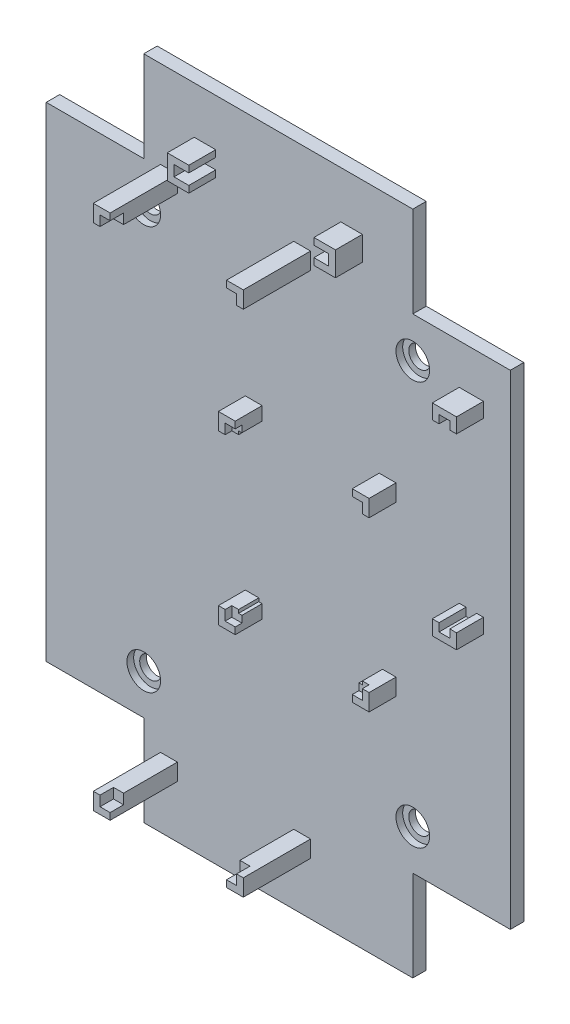
SolidWorks part; units mm, degrees
ref_plane "Front Plane" through (0, 0, 0) normal (0, 0, 1) x (1, 0, 0)
ref_plane "Top Plane" through (0, 0, 0) normal (0, 1, 0) x (1, 0, 0)
ref_plane "Right Plane" through (0, 0, 0) normal (1, 0, 0) x (0, 0, -1)
sketch3d "3DSketch1"
  line L12 (0, 85.2094, 0) -> (0, -85.2094, 0) construction
  line L13 (-20, 20.8016, 0) -> (20, 20.8016, 0)
  line L14 (20, 20.8016, 0) -> (20, 7.3016, 0)
  line L15 (20, 7.3016, 0) -> (34.5, 7.3016, 0)
  line L16 (34.5, 7.3016, 0) -> (34.5, -64.6984, 0)
  line L17 (34.5, -64.6984, 0) -> (20, -64.6984, 0)
  line L18 (20, -64.6984, 0) -> (20, -78.1984, 0)
  line L19 (20, -78.1984, 0) -> (-20, -78.1984, 0)
  line L20 (-85.4416, -28.6984, 0) -> (102.9541, -28.6984, 0) construction
  line L21 (-20, -64.6984, 0) -> (-20, -78.1984, 0)
  line L22 (-34.5, -64.6984, 0) -> (-20, -64.6984, 0)
  line L23 (-20, 7.3016, 0) -> (-34.5, 7.3016, 0)
  line L24 (-34.5, 7.3016, 0) -> (-34.5, -64.6984, 0)
  line L25 (-20, 20.8016, 0) -> (-20, 7.3016, 0)
  line L26 (0, 0, 58.811) -> (0, 0, -52.3115) construction
  circle A0 centre (-20, 1.3016, 0) radius 1.6
  circle A1 centre (20, 1.3016, 0) radius 1.6
  circle A2 centre (20, -58.6984, 0) radius 1.6
  circle A3 centre (-20, -58.6984, 0) radius 1.6
  point P15 (0, -78.1984, 0)
  point P19 (0, 20.8016, 0)
  point P21 (-20, 1.3016, 1.6)
  point P24 (20, 1.3016, 1.6)
  point P27 (20, -58.6984, 1.6)
  point P30 (-20, -58.6984, 1.6)
  dimension "D10" = 3.2
  dimension "D11" = 3.2
  dimension "D1" = 99
  dimension "D2" = 34.5
  dimension "D3" = 20
  dimension "D4" = 20
  dimension "D5" = 49.5
  dimension "D6" = 72
  dimension "D7" = 13.5
  dimension "D8" = 20
  dimension "D9" = 14.5
  dimension "D12" = 40
  dimension "D13" = 20
  dimension "D14" = 30
  dimension "D15" = 30
extrude "Boss-Extrude1" add sketch "3DSketch1" along direction (0, 0, -1) on the side against the normal blind 2 contours L21 L19 L18 L17 L16 L15 L14 L13 L25 L23 L24 L22
sketch "Sketch2" plane through (0, 0, 0) normal (0, 0, 1) x (1, 0, 0)
  line L0 (0, 0) -> (0, -83.2949) construction
  line L1 (-48.7659, -28.6984) -> (71.6911, -28.6984) construction
  line L3 (-20, 7.3016) -> (-34.5, 7.3016) construction
  circle A0 centre (-20, 1.3016) radius 1.6
  circle A1 centre (20, 1.3016) radius 1.6
  circle A2 centre (20, -58.6984) radius 1.6
  circle A3 centre (-20, -58.6984) radius 1.6
  point P0 (-20, 1.3016)
  point P10 (20, 1.3016)
  point P12 (-20, -58.6984)
  point P13 (20, -58.6984)
  dimension "D4" = 3.2
  dimension "D5" = 3.2
  dimension "D6" = 3.2
  dimension "D7" = 3.2
  dimension "D1" = 36
  dimension "D2" = 30
  dimension "D3" = 20
extrude "Cut-Extrude1" cut sketch "Sketch2" against normal blind 2
sketch "Sketch4" plane through (0, 0, 0) normal (0, 0, 1) x (1, 0, 0)
sketch "Sketch5" plane through (0, 0, 0) normal (0, 0, 1) x (1, 0, 0)
  circle A0 centre (-20, 1.3016) radius 2.5
  circle A1 centre (20, 1.3016) radius 2.5
  circle A2 centre (20, -58.6984) radius 2.5
  circle A3 centre (-20, -58.6984) radius 2.5
  dimension "D1" = 5
  dimension "D2" = 5
  dimension "D3" = 5
  dimension "D4" = 5
extrude "Cut-Extrude2" cut sketch "Sketch5" against normal blind 1
sketch "Sketch6" plane through (0, 0, 0) normal (0, 0, 1) x (1, 0, 0)
  line L1 (-11.5, 12.8016) -> (11.5, 12.8016)
  line L2 (-11.5, 12.8016) -> (-11.5, 11.2016)
  line L3 (-11.5, 11.2016) -> (11.5, 11.2016)
  line L4 (11.5, 12.8016) -> (11.5, 11.2016)
  line L5 (20, 20.8016) -> (20, 7.3016) construction
  line L6 (-20, 20.8016) -> (20, 20.8016) construction
  line L8 (-12.5, 13.8016) -> (12.5, 13.8016)
  line L9 (-12.5, 13.8016) -> (-12.5, 10.2016)
  line L10 (-12.5, 10.2016) -> (12.5, 10.2016)
  line L11 (12.5, 13.8016) -> (12.5, 10.2016)
  point P6 (11.5, 12.0016)
  point P13 (-11.5, 12.0016)
  dimension "D1" = 23
  dimension "D2" = 1.6
  dimension "D3" = 8.5
  dimension "D4" = 8
  dimension "D5" = 1
  dimension "D6" = 1
  dimension "D7" = 1
  dimension "D8" = 1
extrude "Boss-Extrude2" add sketch "Sketch6" along normal blind 4
sketch "Sketch7" plane through (0, 13.8016, 0) normal (0, 1, 0) x (1, 0, 0)
  line L0 (12.5, 0) -> (-12.5, 0) construction
  line L1 (-9.3, 0) -> (9.3, 0)
  line L2 (-9.3, 0) -> (-9.3, -4)
  line L3 (-9.3, -4) -> (9.3, -4)
  line L4 (9.3, 0) -> (9.3, -4)
  line L5 (12.5, -4) -> (-12.5, -4) construction
  line L6 (-12.5, -4) -> (-12.5, 0) construction
  line L7 (12.5, -4) -> (12.5, 0) construction
  dimension "D1" = 3.2
  dimension "D2" = 3.2
extrude "Cut-Extrude3" cut sketch "Sketch7" against normal blind 15 contours L2 L3 L4 L1
sketch "Sketch9" plane through (0, 0, 0) normal (0, 0, 1) x (1, 0, 0)
  line L0 (20, 7.3016) -> (34.5, 7.3016) construction
  line L1 (27.9, 0.3016) -> (29.5, 0.3016)
  line L2 (27.9, 0.3016) -> (27.9, -27.6984)
  line L3 (27.9, -27.6984) -> (29.5, -27.6984)
  line L4 (29.5, 0.3016) -> (29.5, -27.6984)
  line L5 (34.5, 7.3016) -> (34.5, -64.6984) construction
  line L7 (26.9, 1.3016) -> (30.5, 1.3016)
  line L8 (26.9, 1.3016) -> (26.9, -28.6984)
  line L9 (26.9, -28.6984) -> (30.5, -28.6984)
  line L10 (30.5, 1.3016) -> (30.5, -28.6984)
  point P4 (29.5, -27.6984)
  dimension "D1" = 28
  dimension "D2" = 1.6
  dimension "D3" = 35
  dimension "D4" = 5
  dimension "D5" = 1
  dimension "D6" = 1
  dimension "D7" = 1
  dimension "D8" = 1
extrude "Boss-Extrude4" add sketch "Sketch9" along normal blind 4
sketch "Sketch10" plane through (30.5, 0, 0) normal (1, 0, 0) x (0, 0, -1)
  line L0 (-4, -28.6984) -> (-4, 1.3016) construction
  line L1 (-4, -0.8984) -> (0, -0.8984)
  line L2 (-4, -0.8984) -> (-4, -26.4984)
  line L3 (-4, -26.4984) -> (0, -26.4984)
  line L4 (0, -0.8984) -> (0, -26.4984)
  line L5 (0, 7.3016) -> (0, -64.6984) construction
  line L6 (-4, 1.3016) -> (0, 1.3016) construction
  line L7 (-4, -28.6984) -> (0, -28.6984) construction
  point P10 (-2, 1.3016)
  dimension "D1" = 2.2
  dimension "D2" = 2.2
extrude "Cut-Extrude4" cut sketch "Sketch10" against normal blind 4
sketch "Sketch11" plane through (0, 0, 0) normal (0, 0, 1) x (1, 0, 0)
  line L0 (34.5, 7.3016) -> (34.5, -64.6984) construction
  line L1 (-3.9, -16.6984) -> (16.5, -16.6984)
  line L2 (-3.9, -16.6984) -> (-3.9, -42.1984)
  line L3 (-3.9, -42.1984) -> (16.5, -42.1984)
  line L4 (16.5, -16.6984) -> (16.5, -42.1984)
  line L5 (20, -78.1984) -> (-20, -78.1984) construction
  line L7 (-4.9, -15.6984) -> (17.5, -15.6984)
  line L8 (-4.9, -15.6984) -> (-4.9, -43.1984)
  line L9 (-4.9, -43.1984) -> (17.5, -43.1984)
  line L10 (17.5, -15.6984) -> (17.5, -43.1984)
  dimension "D1" = 25.5
  dimension "D2" = 20.4
  dimension "D3" = 18
  dimension "D4" = 36
  dimension "D5" = 1
  dimension "D6" = 1
  dimension "D7" = 1
  dimension "D8" = 1
extrude "Boss-Extrude5" add sketch "Sketch11" along normal blind 4
sketch "Sketch12" plane through (0, 0, 0) normal (0, 0, 1) x (1, 0, 0)
  line L9 (-3.9, -16.6984) -> (16.5, -16.6984)
  line L10 (-3.9, -16.6984) -> (-3.9, -42.1984)
  line L11 (-3.9, -42.1984) -> (16.5, -42.1984)
  line L12 (16.5, -16.6984) -> (16.5, -42.1984)
extrude "Boss-Extrude6" add sketch "Sketch12" along normal blind 3
sketch "Sketch13" plane through (0, 0, 3) normal (0, 0, 1) x (1, 0, 0)
  line L0 (16.5, -16.6984) -> (-3.9, -16.6984) construction
  line L1 (-2.9, -17.6984) -> (15.5, -17.6984)
  line L2 (-2.9, -17.6984) -> (-2.9, -41.1984)
  line L3 (-2.9, -41.1984) -> (15.5, -41.1984)
  line L4 (15.5, -17.6984) -> (15.5, -41.1984)
  line L5 (16.5, -42.1984) -> (16.5, -16.6984) construction
  line L6 (-3.9, -42.1984) -> (16.5, -42.1984) construction
  line L7 (-3.9, -16.6984) -> (-3.9, -42.1984) construction
  dimension "D1" = 1
  dimension "D2" = 1
  dimension "D3" = 1
  dimension "D4" = 1
extrude "Cut-Extrude5" cut sketch "Sketch13" against normal blind 3
sketch "Sketch14" plane through (-4.9, 0, 0) normal (-1, 0, 0) x (0, 0, 1)
  line L0 (0, -15.6984) -> (0, -43.1984) construction
  line L1 (0, -18.1984) -> (4, -18.1984)
  line L2 (0, -18.1984) -> (0, -40.6984)
  line L3 (0, -40.6984) -> (4, -40.6984)
  line L4 (4, -18.1984) -> (4, -40.6984)
  line L5 (4, -15.6984) -> (4, -43.1984) construction
  line L6 (4, -15.6984) -> (0, -15.6984) construction
  line L7 (4, -43.1984) -> (0, -43.1984) construction
  dimension "D1" = 2.5
  dimension "D2" = 2.5
extrude "Cut-Extrude6" cut sketch "Sketch14" against normal blind 30 contours L1 L4 L3 L2
sketch "Sketch15" plane through (0, -43.1984, 0) normal (0, -1, 0) x (1, 0, 0)
  line L0 (-4.9, 4) -> (17.5, 4) construction
  line L1 (-2.4, 4) -> (15, 4)
  line L2 (-2.4, 4) -> (-2.4, 0)
  line L3 (-2.4, 0) -> (15, 0)
  line L4 (15, 4) -> (15, 0)
  line L5 (-4.9, 0) -> (17.5, 0) construction
  line L6 (-4.9, 4) -> (-4.9, 0) construction
  line L7 (17.5, 4) -> (17.5, 0) construction
  dimension "D1" = 2.5
  dimension "D2" = 2.5
extrude "Cut-Extrude7" cut sketch "Sketch15" against normal blind 30
sketch "Sketch16" plane through (0, 0, 0) normal (0, 0, 1) x (1, 0, 0)
  line L1 (-16.5, 6.8016) -> (3.8, 6.8016)
  line L2 (-16.5, 6.8016) -> (-16.5, -69.3984)
  line L3 (-16.5, -69.3984) -> (3.8, -69.3984)
  line L4 (3.8, 6.8016) -> (3.8, -69.3984)
  line L6 (-34.5, 7.3016) -> (-34.5, -64.6984) construction
  line L7 (-20, 20.8016) -> (20, 20.8016) construction
  line L9 (-17.5, 7.8016) -> (4.8, 7.8016)
  line L10 (-17.5, 7.8016) -> (-17.5, -70.3984)
  line L11 (-17.5, -70.3984) -> (4.8, -70.3984)
  line L12 (4.8, 7.8016) -> (4.8, -70.3984)
  dimension "D1" = 76.2
  dimension "D2" = 18
  dimension "D3" = 14
  dimension "D4" = 20.3
  dimension "D5" = 1
  dimension "D6" = 1
  dimension "D7" = 1
  dimension "D8" = 1
extrude "Boss-Extrude7" add sketch "Sketch16" along normal blind 10
sketch "Sketch17" plane through (0, -70.3984, 0) normal (0, -1, 0) x (1, 0, 0)
  line L0 (-17.5, 10) -> (4.8, 10) construction
  line L1 (-15, 10) -> (2.3, 10)
  line L2 (-15, 10) -> (-15, 0)
  line L3 (-15, 0) -> (2.3, 0)
  line L4 (2.3, 10) -> (2.3, 0)
  line L5 (-17.5, 0) -> (4.8, 0) construction
  line L6 (-17.5, 10) -> (-17.5, 0) construction
  line L7 (4.8, 10) -> (4.8, 0) construction
  dimension "D1" = 2.5
  dimension "D2" = 2.5
extrude "Cut-Extrude8" cut sketch "Sketch17" against normal blind 10
sketch "Sketch18" plane through (0, 7.8016, 0) normal (0, 1, 0) x (1, 0, 0)
  line L0 (-20, 0) -> (20, 0) construction
  line L1 (-15, 0) -> (2.3, 0)
  line L2 (-15, 0) -> (-15, -10)
  line L3 (-15, -10) -> (2.3, -10)
  line L4 (2.3, 0) -> (2.3, -10)
  line L5 (4.8, -10) -> (-17.5, -10) construction
  line L6 (-17.5, -10) -> (-17.5, 0) construction
  line L7 (4.8, -10) -> (4.8, 0) construction
  dimension "D1" = 2.5
  dimension "D2" = 2.5
extrude "Cut-Extrude9" cut sketch "Sketch18" against normal up to next contours L2 L3 L4 L1
sketch "Sketch19" plane through (-17.5, 0, 0) normal (-1, 0, 0) x (0, 0, 1)
  line L0 (0, 7.8016) -> (0, 1.3016) construction
  line L1 (0, 5.3016) -> (10, 5.3016)
  line L2 (0, 5.3016) -> (0, -67.8984)
  line L3 (0, -67.8984) -> (10, -67.8984)
  line L4 (10, 5.3016) -> (10, -67.8984)
  line L5 (10, 7.8016) -> (10, -70.3984) construction
  line L6 (10, 7.8016) -> (0, 7.8016) construction
  line L7 (10, -70.3984) -> (0, -70.3984) construction
  dimension "D1" = 2.5
  dimension "D2" = 2.5
extrude "Cut-Extrude10" cut sketch "Sketch19" against normal up to next
sketch "Sketch20" plane through (4.8, 0, 0) normal (1, 0, 0) x (0, 0, -1)
  line L0 (-10, -70.3984) -> (-10, 7.8016) construction
  line L1 (-10, 5.3016) -> (0, 5.3016)
  line L2 (-10, 5.3016) -> (-10, -67.8984)
  line L3 (-10, -67.8984) -> (0, -67.8984)
  line L4 (0, 5.3016) -> (0, -67.8984)
  line L5 (0, -70.3984) -> (0, 7.8016) construction
  line L6 (-10, 7.8016) -> (0, 7.8016) construction
  line L7 (-10, -70.3984) -> (0, -70.3984) construction
  dimension "D1" = 2.5
  dimension "D2" = 2.5
extrude "Cut-Extrude11" cut sketch "Sketch20" against normal up to next contours L1 L4 L3 L2
sketch "Sketch21" plane through (0, 0, 0) normal (0, 0, 1) x (1, 0, 0)
  line L1 (-16.5, 6.8016) -> (-15, 6.8016)
  line L2 (-16.5, 6.8016) -> (-16.5, 5.3016)
  line L3 (-16.5, 5.3016) -> (-15, 5.3016)
  line L4 (-15, 6.8016) -> (-15, 5.3016)
  line L8 (3.8, 6.8016) -> (2.3, 6.8016)
  line L9 (3.8, 6.8016) -> (3.8, 5.3016)
  line L10 (3.8, 5.3016) -> (2.3, 5.3016)
  line L11 (2.3, 6.8016) -> (2.3, 5.3016)
  line L12 (3.8, -69.3984) -> (2.3, -69.3984)
  line L13 (3.8, -69.3984) -> (3.8, -67.8984)
  line L14 (3.8, -67.8984) -> (2.3, -67.8984)
  line L15 (2.3, -69.3984) -> (2.3, -67.8984)
  line L16 (-16.5, -69.3984) -> (-15, -69.3984)
  line L17 (-16.5, -69.3984) -> (-16.5, -67.8984)
  line L18 (-16.5, -67.8984) -> (-15, -67.8984)
  line L19 (-15, -69.3984) -> (-15, -67.8984)
  dimension "D1" = 1.5
  dimension "D2" = 1.5
  dimension "D3" = 1.5
  dimension "D4" = 1.5
  dimension "D5" = 1.5
  dimension "D6" = 1.5
  dimension "D7" = 1.5
  dimension "D8" = 1.5
extrude "Boss-Extrude8" add sketch "Sketch21" along normal blind 8
